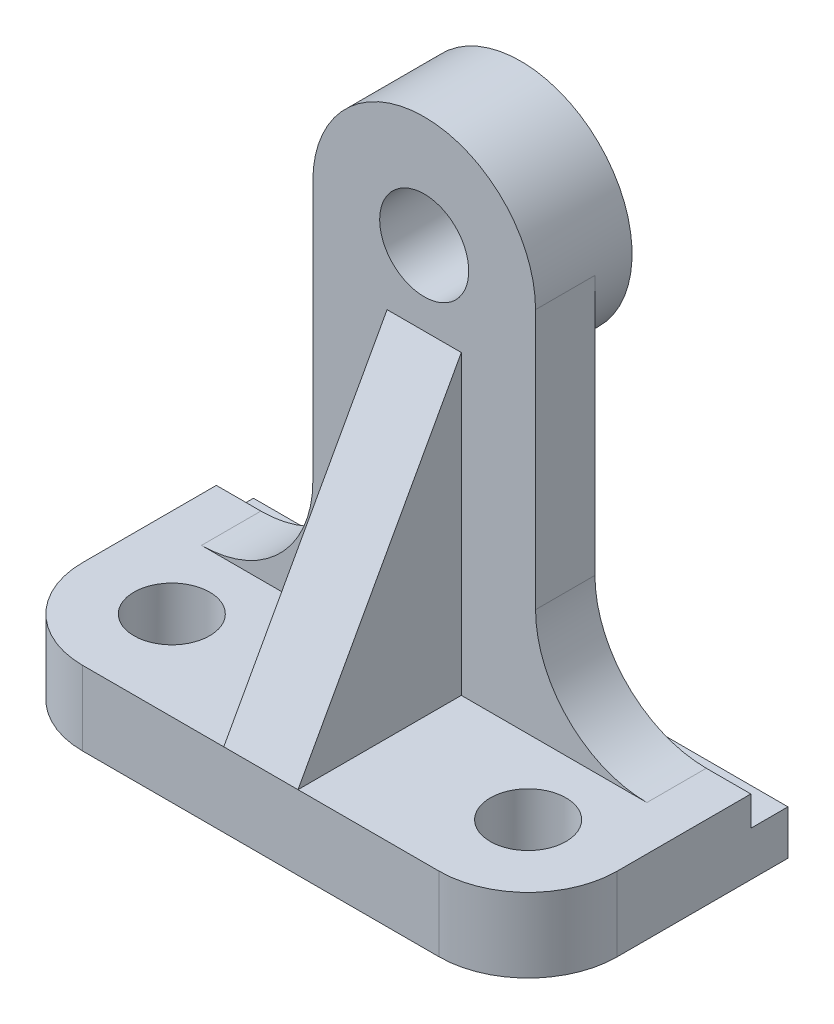
SolidWorks part; units mm, degrees
ref_plane "Front Plane" through (0, 0, 0) normal (0, 0, 1) x (1, 0, 0)
ref_plane "Top Plane" through (0, 0, 0) normal (0, 1, 0) x (1, 0, 0)
ref_plane "Right Plane" through (0, 0, 0) normal (1, 0, 0) x (0, 0, -1)
sketch "Sketch1" plane through (0, 0, 0) normal (0, 1, 0) x (1, 0, 0)
  line L1 (-36, -17.5) -> (36, -17.5)
  line L2 (-36, -17.5) -> (-36, 17.5)
  line L3 (-36, 17.5) -> (36, 17.5)
  line L4 (36, -17.5) -> (36, 17.5)
  line L5 (-36, -17.5) -> (36, 17.5) construction
  line L6 (-36, 17.5) -> (36, -17.5) construction
  point P0 (0, 0)
  dimension "D1" = 72
  dimension "35" = 35
extrude "Boss-Extrude1" add sketch "Sketch1" along normal blind 10
fillet "Fillet1" radius 12 2 edges at (36, 5, 17.5) (-36, 5, 17.5)
sketch "Sketch2" plane through (36, 0, 0) normal (1, 0, 0) x (0, 0, -1)
  line L1 (17.5, 10) -> (12.5, 10)
  line L2 (17.5, 10) -> (17.5, 6)
  line L3 (17.5, 6) -> (12.5, 6)
  line L4 (12.5, 10) -> (12.5, 6)
  dimension "D1" = 4
  dimension "5" = 5
extrude "Cut-Extrude1" cut sketch "Sketch2" against normal through all
sketch "Sketch3" plane through (0, 0, -12.5) normal (0, 0, -1) x (-1, 0, 0)
  line L0 (15, 10) -> (-15, 10)
  line L1 (36, 10) -> (-36, 10) construction
  line L2 (-15, 10) -> (-15, 60)
  line L3 (15, 60) -> (15, 10)
  arc A0 (-15, 60) -> (15, 60) centre (0, 60) cw
  circle A1 centre (0, 60) radius 6
  point P8 (0, 0)
  point P10 (0, 0)
  point P13 (0, 0)
  dimension "D1" = 12
  dimension "D2" = 15
  dimension "D3" = 50
extrude "Boss-Extrude2" add sketch "Sketch3" against normal blind 8
fillet "Fillet2" radius 15 1 edges at (15, 10, -8.5)
fillet "Fillet3" radius 15 1 edges at (-15, 10, -8.5)
hole_wizard "M12 Tapped Hole1" positions "Sketch6" profile "Sketch5" tap size "M12" standard "DIN" end condition up to next
sketch "Sketch6" plane through (0, 10, 0) normal (0, 1, 0) x (1, 0, 0)
  point P0 (24, -5.5)
  point P3 (-24, -5.5)
sketch "Sketch5" plane through (24, 10, 5.5) normal (1, 0, 0) x (0, 0, 1)
  line L0 (0, 0) -> (0, 10)
  line L1 (0, 10) -> (5.1, 10)
  line L2 (5.1, 10) -> (5.1, 0)
  line L5 (5.1, 0) -> (0, 0)
  line L11 (0, -6.35) -> (0, 107.95) construction
  dimension "Thru Tap Drill Dia." = 10.2
  dimension "Thru Tap Drill Depth" = 10
cosmetic thread "Hole Thread1" parameters "D2"=12
cosmetic thread "Hole Thread2" parameters "D2"=12
sketch "Sketch7" plane through (0, 0, -12.5) normal (0, 0, -1) x (-1, 0, 0)
  circle A0 centre (0, 60) radius 15
  circle A1 centre (0, 60) radius 6 construction
  circle A2 centre (0, 60) radius 6
extrude "Boss-Extrude3" add sketch "Sketch7" along normal blind 5
sketch "Sketch8" plane through (0, 0, 0) normal (1, 0, 0) x (0, 0, -1)
  line L0 (-17.5, 10) -> (4.5, 50)
  line L1 (4.5, 60) -> (4.5, 25) construction
  dimension "D1" = 40
rib "Rib1" sketch "Sketch8" sketch "Sketch8" thickness 10 extrusion direction parallel to sketch draft on no parameters "D1"=10
